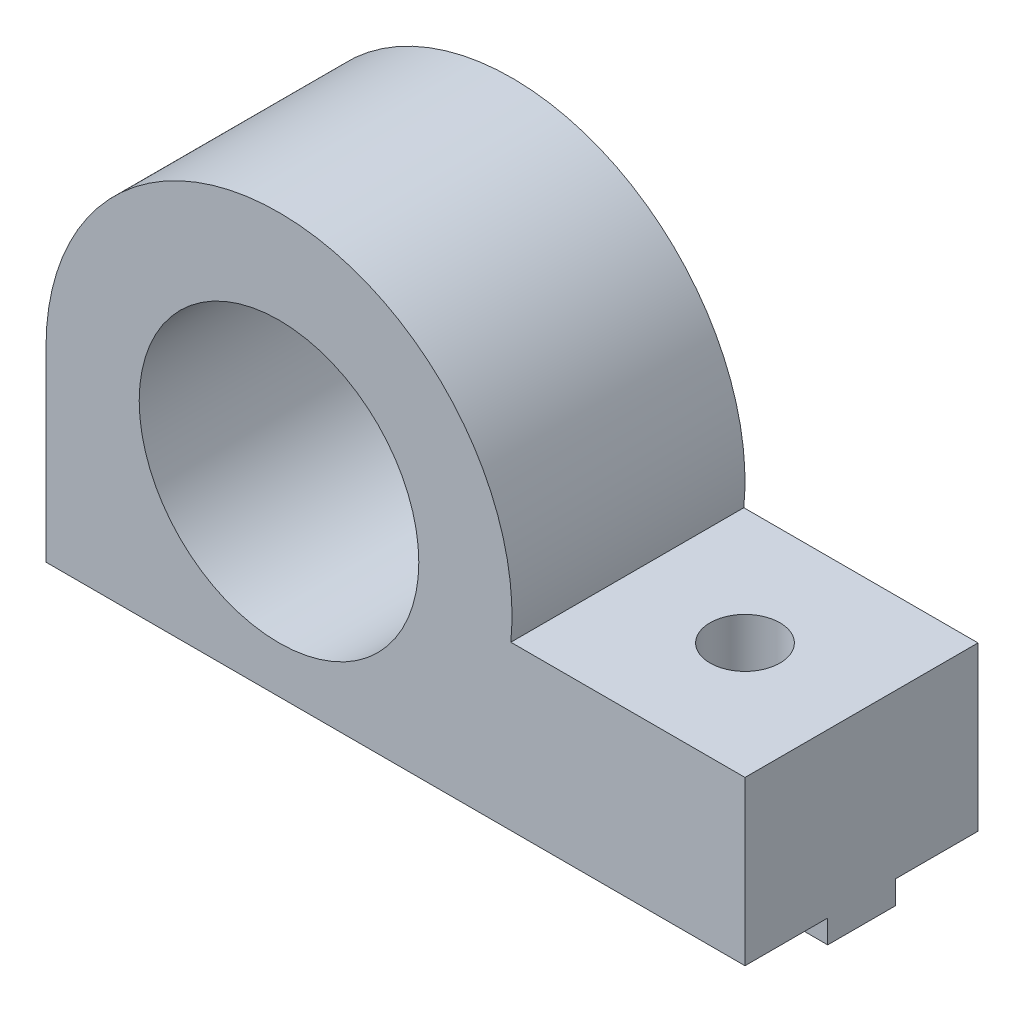
SolidWorks part; units mm, degrees
ref_plane "Front Plane" through (0, 0, 0) normal (0, 0, 1) x (1, 0, 0)
ref_plane "Top Plane" through (0, 0, 0) normal (0, 1, 0) x (1, 0, 0)
ref_plane "Right Plane" through (0, 0, 0) normal (1, 0, 0) x (0, 0, -1)
sketch "Sketch1" plane through (0, 0, 0) normal (0, 0, 1) x (1, 0, 0)
  line L0 (-10, 0) -> (-10, -8)
  line L1 (20, -8) -> (20, -1)
  line L3 (-10, -8) -> (20, -8)
  line L4 (20, -1) -> (9.9499, -1)
  arc A0 (-10, 0) -> (9.9499, -1) centre (0, 0) cw
  circle A1 centre (0, 0) radius 6
  dimension "D1" = 12
  dimension "D2" = 10
  dimension "D3" = 8
  dimension "D4" = 7
  dimension "D5" = 30
extrude "Main" add sketch "Sketch1" along normal blind 10
sketch "Sketch3" plane through (0, -8, 0) normal (0, -1, 0) x (-1, 0, 0)
  line L0 (10, -10) -> (10, 0) construction
  line L1 (10, -6.45) -> (-20, -6.45)
  line L2 (10, -6.45) -> (10, -3.55)
  line L3 (10, -3.55) -> (-20, -3.55)
  line L4 (-20, -6.45) -> (-20, -3.55)
  line L5 (-20, -10) -> (-20, 0) construction
  line L6 (10, 0) -> (-20, 0) construction
  dimension "D1" = 2.9
  dimension "D2" = 3.55
extrude "MakerBeamRectangularGuide" add sketch "Sketch3" along normal blind 1
sketch "Sketch4" plane through (0, -1, 0) normal (0, 1, 0) x (1, 0, 0)
  line L0 (20, -10) -> (9.9499, -10) construction
  line L1 (20, -10) -> (20, 0) construction
  circle A0 centre (15, -5) radius 1.5
  dimension "D1" = 3
  dimension "D2" = 5
  dimension "D3" = 5
extrude "MakerBeamFixHole" cut sketch "Sketch4" against normal through all
